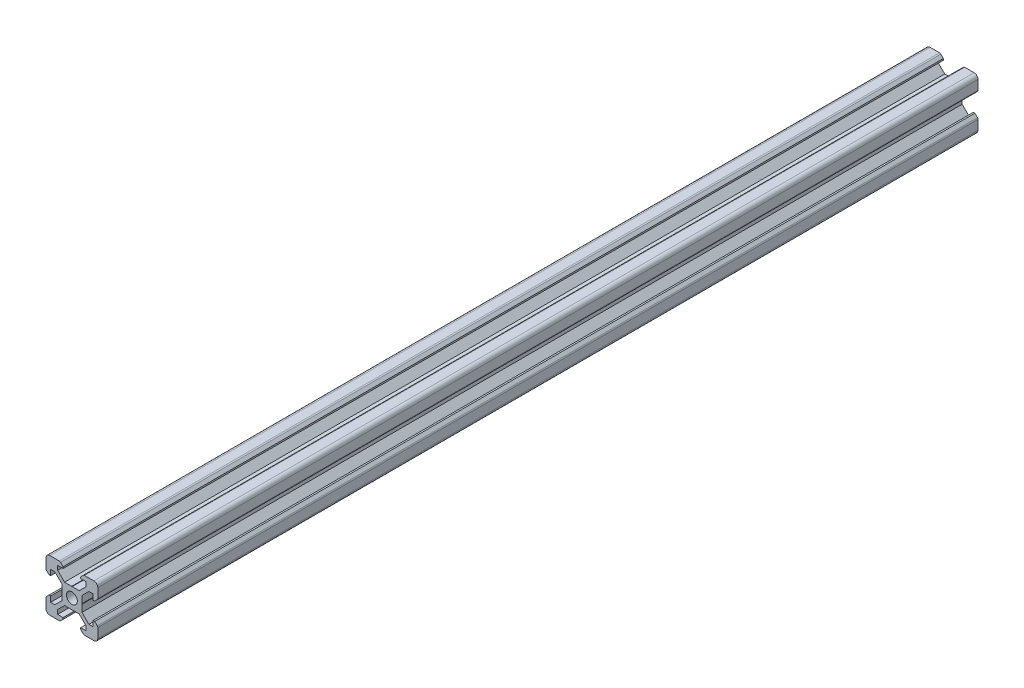
SolidWorks part; units mm, degrees
ref_plane "Front" through (0, 0, 0) normal (0, 0, 1) x (1, 0, 0)
ref_plane "Top" through (0, 0, 0) normal (0, 1, 0) x (1, 0, 0)
ref_plane "Right" through (0, 0, 0) normal (1, 0, 0) x (0, 0, -1)
sketch "Sketch1" plane through (0, 0, 0) normal (0, 0, 1) x (1, 0, 0)
  line L0 (-8.5, 10) -> (-10, 8.5) construction
  line L1 (-8.5, 10) -> (-4.8628, 10)
  line L2 (-10, 8.5) -> (-10, 4.8628)
  line L3 (-8.5, -10) -> (-4.8628, -10)
  line L4 (10, 8.5) -> (10, 4.8628)
  line L5 (-10, 10) -> (10, -10) construction
  line L6 (-10, -10) -> (10, 10) construction
  line L7 (-5.5, -8.2) -> (-3.3865, -8.2)
  line L8 (-8.2, -5.5) -> (-8.2, -3.3865)
  line L9 (-5.5, 8.2) -> (-3.3865, 8.2)
  line L10 (8.2, -5.5) -> (8.2, -3.3865)
  line L11 (-3.9005, 2.8395) -> (-6.561, 5.5)
  line L12 (-6.561, 5.5) -> (-8.2, 5.5)
  line L13 (-2.8395, -3.9005) -> (-0.1, -3.9005)
  line L14 (-3.9005, -2.8395) -> (-3.9005, -0.1)
  line L15 (-2.8395, 3.9005) -> (-0.1, 3.9005)
  line L16 (3.9005, -2.8395) -> (3.9005, -0.1)
  line L17 (-8.2, 3.3865) -> (-8.81, 3.3865)
  line L18 (-8.81, 3.3865) -> (-9.7976, 4.3741)
  line L19 (8.5, 10) -> (10, 8.5) construction
  line L20 (-2.8395, 3.9005) -> (-5.5, 6.561)
  line L21 (-5.5, 6.561) -> (-5.5, 8.2)
  line L22 (-3.3865, 8.2) -> (-3.3865, 8.81)
  line L23 (-3.3865, 8.81) -> (-4.3741, 9.7976)
  line L24 (0, 24.069) -> (0, -33.8154) construction
  line L25 (3.3865, 8.81) -> (4.3741, 9.7976)
  line L26 (3.3865, 8.2) -> (3.3865, 8.81)
  line L27 (5.5, 6.561) -> (5.5, 8.2)
  line L28 (2.8395, 3.9005) -> (5.5, 6.561)
  line L29 (3.3865, 8.2) -> (5.5, 8.2)
  line L30 (4.8628, 10) -> (8.5, 10)
  line L31 (-0.1, 3.9005) -> (0, 3.8005)
  line L32 (0.1, 3.9005) -> (0, 3.8005)
  line L33 (0.1, 3.9005) -> (2.8395, 3.9005)
  line L34 (25.9287, 0) -> (-28.3459, 0) construction
  line L35 (-0.1, -3.9005) -> (0, -3.8005)
  line L36 (0.1, -3.9005) -> (0, -3.8005)
  line L37 (0.1, -3.9005) -> (2.8395, -3.9005)
  line L38 (-3.9005, 0.1) -> (-3.8005, 0)
  line L39 (-3.8005, 0) -> (-3.9005, -0.1)
  line L40 (-3.9005, 0.1) -> (-3.9005, 2.8395)
  line L41 (3.9005, 0.1) -> (3.8005, 0)
  line L42 (3.8005, 0) -> (3.9005, -0.1)
  line L43 (3.9005, 0.1) -> (3.9005, 2.8395)
  line L44 (8.81, 3.3865) -> (9.7976, 4.3741)
  line L45 (8.2, 3.3865) -> (8.81, 3.3865)
  line L46 (6.561, 5.5) -> (8.2, 5.5)
  line L47 (3.9005, 2.8395) -> (6.561, 5.5)
  line L48 (2.8395, -3.9005) -> (5.5, -6.561)
  line L49 (3.9005, -2.8395) -> (6.561, -5.5)
  line L50 (-2.8395, -3.9005) -> (-5.5, -6.561)
  line L51 (-3.9005, -2.8395) -> (-6.561, -5.5)
  line L52 (6.561, -5.5) -> (8.2, -5.5)
  line L53 (-6.561, -5.5) -> (-8.2, -5.5)
  line L54 (-8.81, -3.3865) -> (-9.7976, -4.3741)
  line L55 (-8.2, -3.3865) -> (-8.81, -3.3865)
  line L56 (8.81, -3.3865) -> (9.7976, -4.3741)
  line L57 (8.2, -3.3865) -> (8.81, -3.3865)
  line L58 (8.2, 3.3865) -> (8.2, 5.5)
  line L59 (10, -4.8628) -> (10, -8.5)
  line L60 (-8.2, 3.3865) -> (-8.2, 5.5)
  line L61 (-10, -4.8628) -> (-10, -8.5)
  line L62 (-3.3865, -8.81) -> (-4.3741, -9.7976)
  line L63 (-3.3865, -8.2) -> (-3.3865, -8.81)
  line L64 (3.3865, -8.81) -> (4.3741, -9.7976)
  line L65 (3.3865, -8.2) -> (3.3865, -8.81)
  line L66 (-5.5, -6.561) -> (-5.5, -8.2)
  line L67 (5.5, -6.561) -> (5.5, -8.2)
  line L68 (3.3865, -8.2) -> (5.5, -8.2)
  line L69 (4.8628, -10) -> (8.5, -10)
  circle A0 centre (0, 0) radius 2.1
  arc A1 (-8.5, 10) -> (-10, 8.5) centre (-8.5, 8.5) ccw
  arc A2 (10, 8.5) -> (8.5, 10) centre (8.5, 8.5) ccw
  arc A3 (-4.3741, 9.7976) -> (-4.8628, 10) centre (-4.8628, 9.3088) ccw
  arc A4 (4.8628, 10) -> (4.3741, 9.7976) centre (4.8628, 9.3088) ccw
  arc A5 (-8.5, -10) -> (-10, -8.5) centre (-8.5, -8.5) cw
  arc A6 (9.7976, 4.3741) -> (10, 4.8628) centre (9.3088, 4.8628) ccw
  arc A7 (-10, 4.8628) -> (-9.7976, 4.3741) centre (-9.3088, 4.8628) ccw
  arc A8 (-10, -4.8628) -> (-9.7976, -4.3741) centre (-9.3088, -4.8628) cw
  arc A9 (9.7976, -4.3741) -> (10, -4.8628) centre (9.3088, -4.8628) cw
  arc A10 (10, -8.5) -> (8.5, -10) centre (8.5, -8.5) cw
  arc A11 (-4.3741, -9.7976) -> (-4.8628, -10) centre (-4.8628, -9.3088) cw
  arc A12 (4.8628, -10) -> (4.3741, -9.7976) centre (4.8628, -9.3088) cw
  point P17 (-9.25, 9.25)
  point P21 (9.25, 9.25)
  dimension "D2" = 4.2
  dimension "D4" = 1.5
  dimension "D3" = 20
  dimension "D5" = 0.529
  dimension "D6" = 6.773
  dimension "D7" = 90
  dimension "D8" = 11
  dimension "D9" = 0.61
  dimension "D10" = 0.1
  dimension "D11" = 0.1
  dimension "D12" = 0.1
  dimension "D13" = 0.1
  dimension "D14" = 5.679
  dimension "D15" = 1.639
  dimension "D16" = 1.8
  dimension "D17" = 90
  dimension "D18" = 6.773
  dimension "D19" = 90
extrude "Boss-Extrude1" add sketch "Sketch1" along normal blind 340
